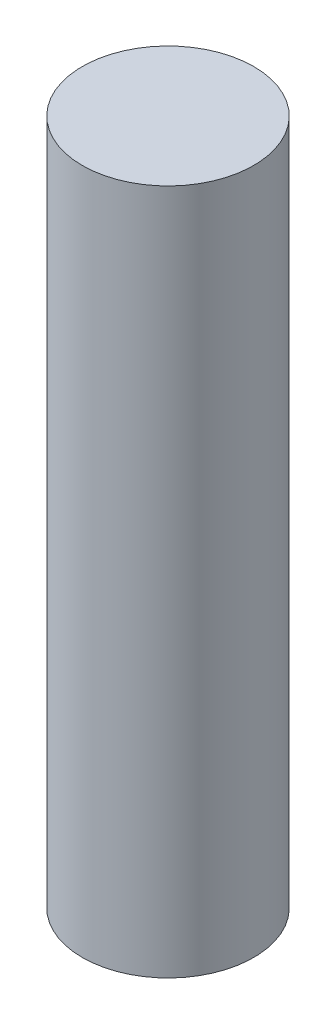
SolidWorks part; units mm, degrees
ref_plane "Front Plane" through (0, 0, 0) normal (0, 0, 1) x (1, 0, 0)
ref_plane "Top Plane" through (0, 0, 0) normal (0, 1, 0) x (1, 0, 0)
ref_plane "Right Plane" through (0, 0, 0) normal (1, 0, 0) x (0, 0, -1)
sketch "Sketch1" plane through (0, 0, 0) normal (0, 1, 0) x (1, 0, 0)
  circle A0 centre (0, 0) radius 6.25
  dimension "D1" = 12.5
extrude "Boss-Extrude1" add sketch "Sketch1" along normal blind 50
